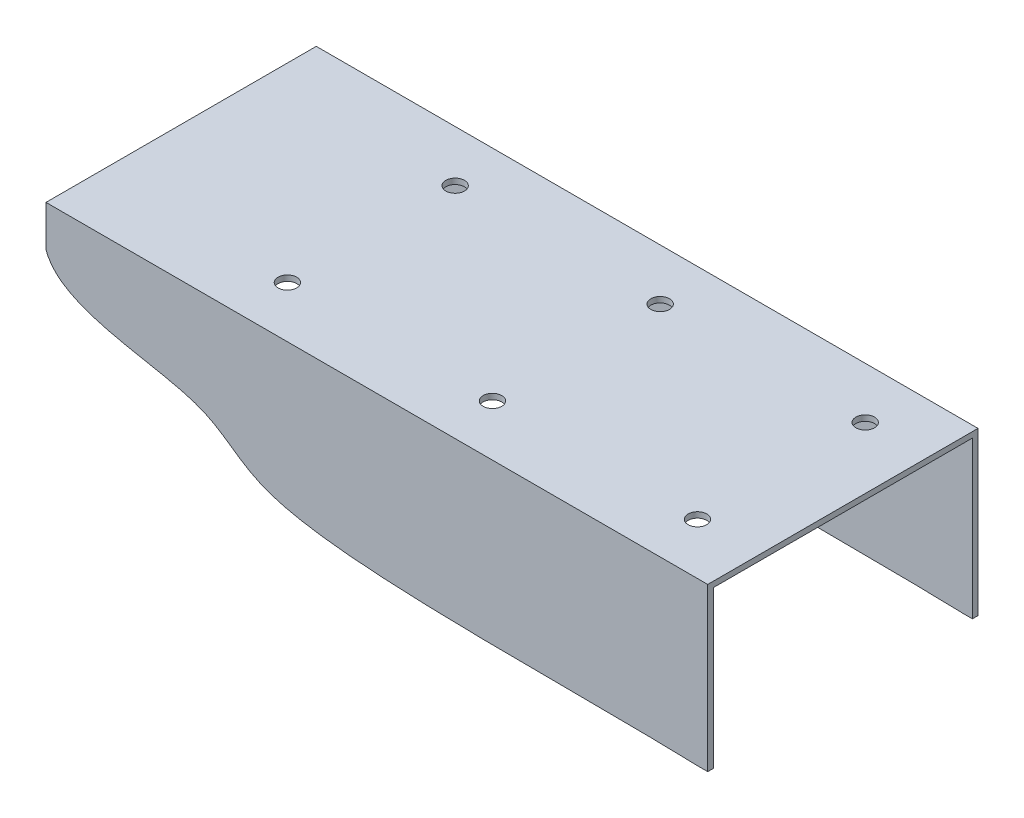
SolidWorks part; units mm, degrees
ref_plane "Спереди" through (0, 0, 0) normal (0, 0, 1) x (1, 0, 0)
ref_plane "Сверху" through (0, 0, 0) normal (0, 1, 0) x (1, 0, 0)
ref_plane "Справа" through (0, 0, 0) normal (1, 0, 0) x (0, 0, -1)
sketch "Эскиз1" plane through (0, 0, 0) normal (1, 0, 0) x (0, 0, -1)
  line L0 (0, 0) -> (0, 87)
  line L1 (0, 87) -> (145, 87)
  line L2 (145, 87) -> (145, 0)
extrude "Вытянуть-Тонкостенный1" add sketch "Эскиз1" along normal blind 355 thin
sketch "Эскиз2" plane through (0, 0, 0) normal (0, 0, 1) x (1, 0, 0)
  line L0 (0, 65.1241) -> (0, 0)
  line L1 (0, 0) -> (0, 87) construction
  line L2 (0, 0) -> (350.2785, 0)
  line L3 (355, 0) -> (0, 0) construction
  spline S0 degree 3 poles (0, 65.1241) (7.9338, 41.7869) (88.8356, 42.672) (115.5486, -4.5707) (275.8086, 2.4518) (350.2785, 0) knots 0 0 0 0 0.332901 0.537301 1 1 1 1
extrude "Вырез-Вытянуть1" cut sketch "Эскиз2" against normal through all
sketch "Эскиз3" plane through (0, 87, 0) normal (0, 1, 0) x (1, 0, 0)
  circle A0 centre (322, 117.5) radius 5
  circle A1 centre (212, 117.5) radius 5
  circle A2 centre (102, 117.5) radius 5
  circle A3 centre (212, 27.5) radius 5
  circle A4 centre (102, 27.5) radius 5
  circle A5 centre (322, 27.5) radius 5
  dimension "D1" = 3
  dimension "D2" = 2
extrude "Вырез-Вытянуть2" cut sketch "Эскиз3" against normal blind 10
